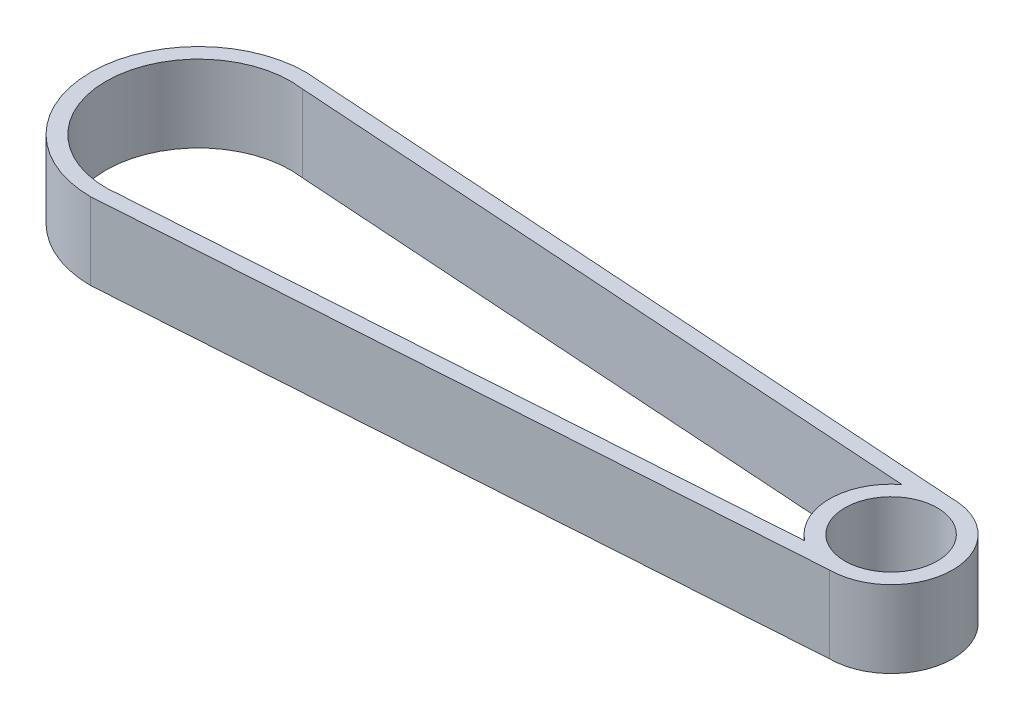
SolidWorks part; units mm, degrees
ref_plane "Front Plane" through (0, 0, 0) normal (0, 0, 1) x (1, 0, 0)
ref_plane "Top Plane" through (0, 0, 0) normal (0, 1, 0) x (1, 0, 0)
ref_plane "Right Plane" through (0, 0, 0) normal (1, 0, 0) x (0, 0, -1)
sketch "Sketch1" plane through (0, 0, 0) normal (0, 1, 0) x (1, 0, 0)
  line L0 (0, 14) -> (90, 8)
  line L1 (0, -14) -> (90, -8)
  line L4 (-0.133, 12.0044) -> (89.867, 6.0044)
  line L5 (-0.133, -12.0044) -> (89.867, -6.0044)
  line L6 (0, 14) -> (0, -14)
  line L7 (90, 8) -> (90, -8)
  circle A0 centre (0, 0) radius 14
  circle A1 centre (90, 0) radius 8
  circle A2 centre (0, 0) radius 12
  circle A3 centre (90, 0) radius 6
  dimension "D1" = 28
  dimension "D2" = 16
  dimension "D3" = 90
  dimension "D4" = 2
  dimension "D5" = 2
  dimension "D6" = 2
extrude "Boss-Extrude1" add sketch "Sketch1" along normal blind 10
